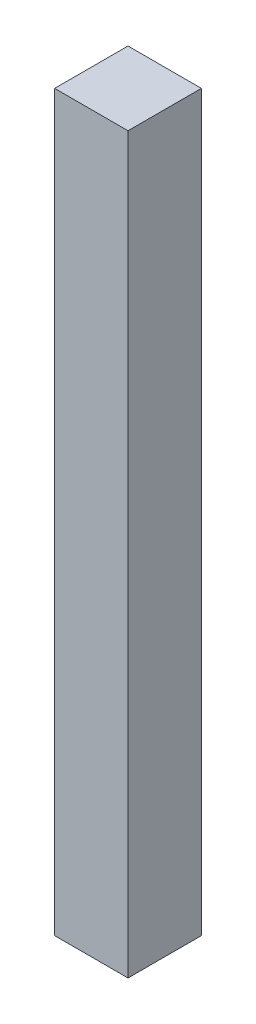
SolidWorks part; units mm, degrees
ref_plane "Front Plane" through (0, 0, 0) normal (0, 0, 1) x (1, 0, 0)
ref_plane "Top Plane" through (0, 0, 0) normal (0, 1, 0) x (1, 0, 0)
ref_plane "Right Plane" through (0, 0, 0) normal (1, 0, 0) x (0, 0, -1)
sketch "Sketch1" plane through (0, 0, 0) normal (0, 1, 0) x (1, 0, 0)
  line L1 (-10, -10) -> (10, -10)
  line L2 (-10, -10) -> (-10, 10)
  line L3 (-10, 10) -> (10, 10)
  line L4 (10, -10) -> (10, 10)
  line L5 (-10, -10) -> (10, 10) construction
  line L6 (-10, 10) -> (10, -10) construction
  point P0 (0, 0)
  dimension "D1" = 20
  dimension "D2" = 20
extrude "Boss-Extrude1" add sketch "Sketch1" along normal blind 200
